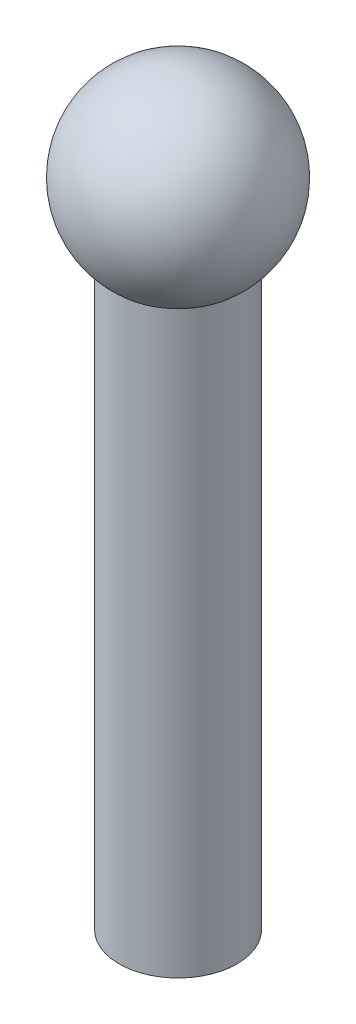
SolidWorks part; units mm, degrees
ref_plane "Front Plane" through (0, 0, 0) normal (0, 0, 1) x (1, 0, 0)
ref_plane "Top Plane" through (0, 0, 0) normal (0, 1, 0) x (1, 0, 0)
ref_plane "Right Plane" through (0, 0, 0) normal (1, 0, 0) x (0, 0, -1)
sketch "Sketch1" plane through (0, 0, 0) normal (0, 0, 1) x (1, 0, 0)
  line L0 (0, 0) -> (0, 15)
  line L1 (0, 7.5) -> (-7.5, 7.5) construction
  arc A1 (0, 15) -> (0, 0) centre (0, 7.5) ccw
  dimension "D1" = 15
revolve "Revolve1" add sketch "Sketch1" angle 360 about L0
ref_plane "Plane1" through (0, 0, 0) normal (0, -1, 0) x (-1, 0, 0)
sketch "Sketch2" plane through (0, 0, 0) normal (0, -1, 0) x (-1, 0, 0)
  circle A0 centre (0, 0) radius 4.755
  dimension "D1" = 9.51
extrude "Boss-Extrude1" add sketch "Sketch2" against normal blind 3 contours A0
ref_plane "Plane2" through (0, 0, 0) normal (0, -1, 0) x (-1, 0, 0)
sketch "Sketch3" plane through (0, 0, 0) normal (0, -1, 0) x (-1, 0, 0)
  circle A0 centre (0, 0) radius 4.755
  dimension "D1" = 9.51
extrude "Boss-Extrude2" add sketch "Sketch3" along normal blind 45 contours A0
